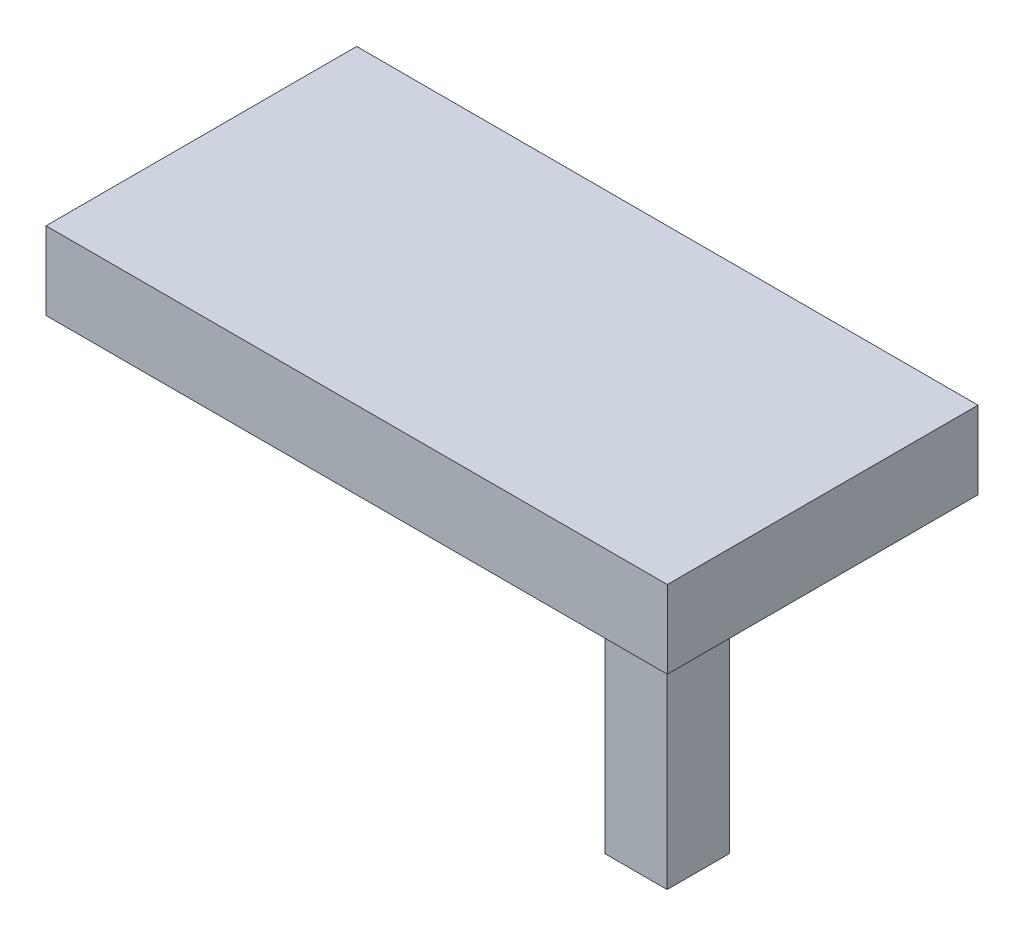
SolidWorks part; units mm, degrees
ref_plane "Front Plane" through (0, 0, 0) normal (0, 0, 1) x (1, 0, 0)
ref_plane "Top Plane" through (0, 0, 0) normal (0, 1, 0) x (1, 0, 0)
ref_plane "Right Plane" through (0, 0, 0) normal (1, 0, 0) x (0, 0, -1)
sketch "Sketch2" plane through (0, 0, 0) normal (0, 1, 0) x (1, 0, 0)
  line L1 (-1000, 500) -> (1000, 500)
  line L2 (-1000, 500) -> (-1000, -500)
  line L3 (-1000, -500) -> (1000, -500)
  line L4 (1000, 500) -> (1000, -500)
  line L5 (-1000, 500) -> (1000, -500) construction
  line L6 (-1000, -500) -> (1000, 500) construction
  point P0 (0, 0)
  dimension "D1" = 2000
  dimension "D2" = 1000
extrude "Boss-Extrude1" add sketch "Sketch2" along normal blind 250
sketch "Sketch3" plane through (0, 0, 0) normal (0, -1, 0) x (1, 0, 0)
  line L4 (-250, -251.5808) -> (-750, -251.5808)
  line L5 (-250, -251.5808) -> (-250, 251.5808)
  line L6 (250, 251.5808) -> (750, 251.5808)
  line L7 (250, 251.5808) -> (250, -251.5808)
  line L8 (250, -251.5808) -> (750, -251.5808)
  line L9 (750, 251.5808) -> (750, -251.5808)
  line L10 (250, 251.5808) -> (750, -251.5808) construction
  line L11 (250, -251.5808) -> (750, 251.5808) construction
  line L12 (-250, 251.5808) -> (-750, 251.5808)
  line L13 (-750, -251.5808) -> (-750, 251.5808)
  line L14 (-250, -251.5808) -> (-750, 251.5808) construction
  line L15 (-250, 251.5808) -> (-750, -251.5808) construction
extrude "Boss-Extrude2" add sketch "Sketch3" along normal blind 100
sketch "Sketch4" plane through (0, -100, 0) normal (0, -1, 0) x (1, 0, 0)
  line L5 (600, -100.6323) -> (400, -100.6323)
  line L6 (600, -100.6323) -> (600, 100.6323)
  line L7 (600, 100.6323) -> (400, 100.6323)
  line L8 (400, -100.6323) -> (400, 100.6323)
  line L9 (600, -100.6323) -> (400, 100.6323) construction
  line L10 (600, 100.6323) -> (400, -100.6323) construction
  point P2 (500, 0)
  dimension "D1" = 200
extrude "Boss-Extrude3" add sketch "Sketch4" along normal blind 900 contours L8 L7 L6 L5
